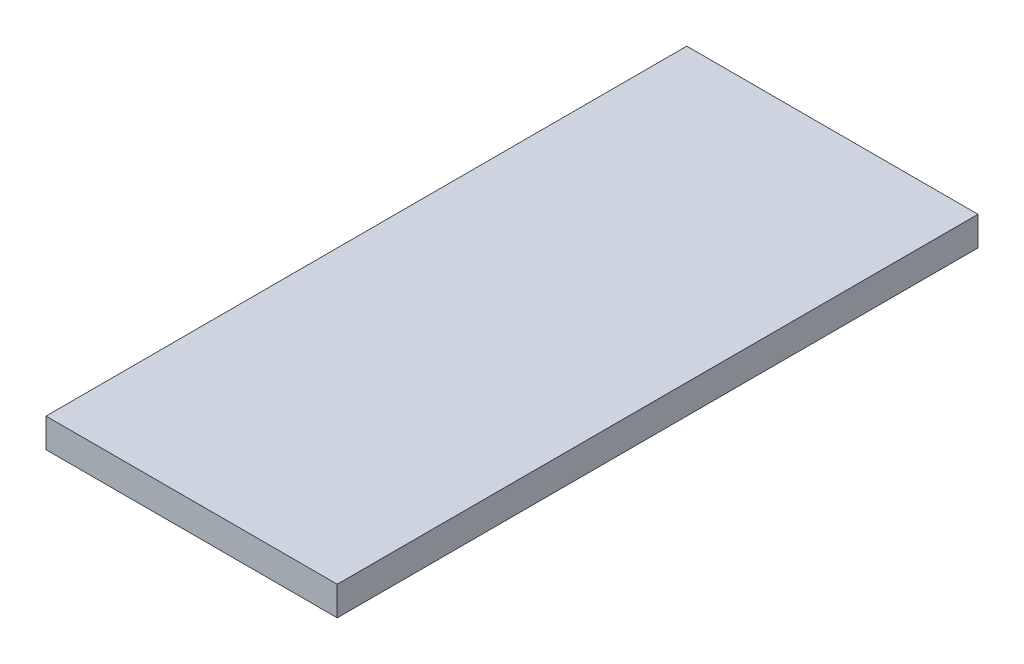
SolidWorks part; units mm, degrees
ref_plane "Front Plane" through (0, 0, 0) normal (0, 0, 1) x (1, 0, 0)
ref_plane "Top Plane" through (0, 0, 0) normal (0, 1, 0) x (1, 0, 0)
ref_plane "Right Plane" through (0, 0, 0) normal (1, 0, 0) x (0, 0, -1)
sketch "Sketch2" plane through (0, 0, 0) normal (0, 1, 0) x (1, 0, 0)
  line L1 (-55.0578, 39.3425) -> (-5.0578, 39.3425)
  line L2 (-55.0578, 39.3425) -> (-55.0578, -70.6575)
  line L3 (-55.0578, -70.6575) -> (-5.0578, -70.6575)
  line L4 (-5.0578, 39.3425) -> (-5.0578, -70.6575)
  line L5 (-30.0578, -70.6575) -> (-30.0578, 39.3425) construction
  line L6 (-55.0578, -15.6575) -> (-5.0578, -15.6575) construction
  point P0 (-30.0578, -15.6575)
  dimension "D1" = 50
  dimension "D2" = 110
extrude "Boss-Extrude1" add sketch "Sketch2" along normal blind 5
